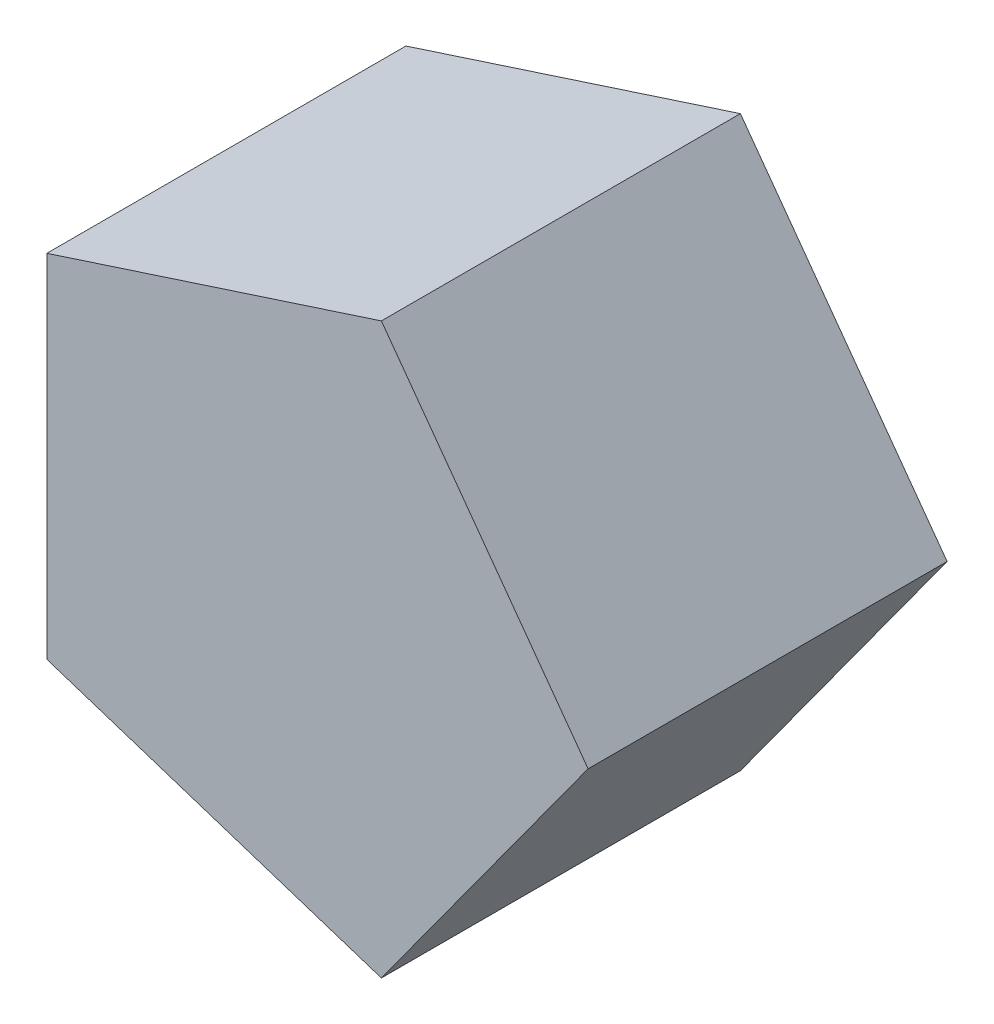
SolidWorks part; units mm, degrees
ref_plane "Piano frontale" through (0, 0, 0) normal (0, 0, 1) x (1, 0, 0)
ref_plane "Piano superiore" through (0, 0, 0) normal (0, 1, 0) x (1, 0, 0)
ref_plane "Piano destro" through (0, 0, 0) normal (1, 0, 0) x (0, 0, -1)
sketch "Schizzo1" plane through (0, 0, 0) normal (0, 0, 1) x (1, 0, 0)
  line L1 (25, 0) -> (7.7254, 23.7764)
  line L2 (7.7254, 23.7764) -> (-20.2254, 14.6946)
  line L3 (-20.2254, 14.6946) -> (-20.2254, -14.6946)
  line L4 (-20.2254, -14.6946) -> (7.7254, -23.7764)
  line L5 (7.7254, -23.7764) -> (25, 0)
  circle A0 centre (0, 0) radius 25 construction
extrude "Estrusione-Estrusione1" add sketch "Schizzo1" along normal blind 30
